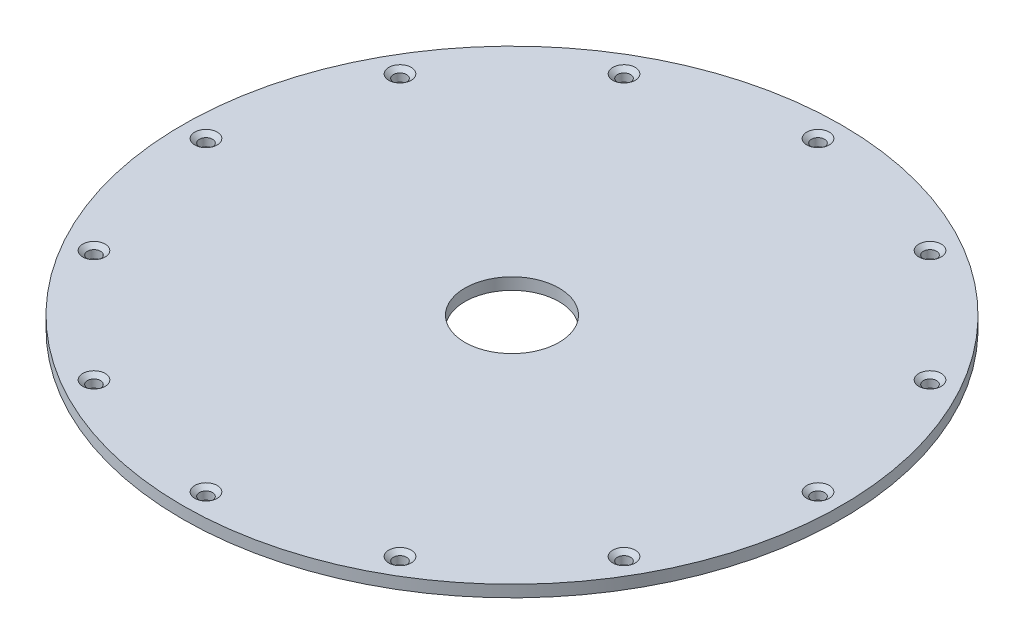
SolidWorks part; units mm, degrees
material "6063-T6"
ref_plane "Front Plane" through (0, 0, 0) normal (0, 0, 1) x (1, 0, 0)
ref_plane "Top Plane" through (0, 0, 0) normal (0, 1, 0) x (1, 0, 0)
ref_plane "Right Plane" through (0, 0, 0) normal (1, 0, 0) x (0, 0, -1)
ref_axis "Axis1" through (0, 55, 0) along (0, -1, 0)
sketch "Sketch1" plane through (0, 0, 0) normal (0, 0, 1) x (1, 0, 0)
  line L0 (-44.45, 0) -> (-6.35, 0)
  line L1 (0, 55) -> (0, -55) construction
  line L2 (-44.45, 0) -> (-44.45, 1.5875)
  line L3 (-44.45, 1.5875) -> (-6.35, 1.5875)
  line L4 (-44.45, 1.5875) -> (-6.35, 1.5875) construction
  line L5 (-6.35, 1.5875) -> (-6.35, 0)
  line L6 (-6.35, 0) -> (0, 0) construction
  line L7 (-44.45, 0) -> (-44.45, 1.5875) construction
  line L8 (-6.35, 1.5875) -> (-6.35, 0) construction
  point P1 (-6.35, 0)
  point P3 (-6.35, 8.9431)
  point P4 (-6.35, 1.5875)
  point P9 (0, 0)
  point P12 (-6.6434, 1.5875)
  point P13 (0, 0)
  point P16 (0, 0)
  point P17 (0, 0)
  point P18 (0, 0)
  point P19 (0, 0)
  point P21 (0, 0)
  point P22 (0, 0)
  point P23 (0, 0)
  point P24 (0, 0)
  point P25 (0, 0)
  point P26 (0, 0)
  point P28 (0, 0)
  point P29 (0, 0)
  point P30 (-6.6747, 0)
revolve "Revolve1" add sketch "Sketch1" angle 360 about axis through (0, 55, 0) along (0, -1, 0)
ref_plane "Hole Location Plane" through (0, 3.175, 0) normal (0, 1, 0) x (1, 0, 0)
sketch "Hole Location" plane through (0, 3.175, 0) normal (0, 1, 0) x (1, 0, 0)
  line L0 (0, 0) -> (-41.275, 0) construction
  circle A0 centre (0, 0) radius 41.275 construction
  dimension "D1" = 82.55
hole_wizard "CSK for #0 Flat Head Machine Screw (100)1" positions "Sketch4" profile "Sketch5" countersink size "#0" standard "ANSI Inch" end condition through all
sketch "Sketch4" plane through (0, 1.5875, 0) normal (0, 1, 0) x (1, 0, 0)
  point P0 (-41.275, 0)
sketch "Sketch5" plane through (-41.275, 1.5875, 0) normal (1, 0, 0) x (0, 0, 1)
  line L0 (0, 0) -> (0, 1.5875)
  line L1 (0, 1.5875) -> (0.889, 1.5875)
  line L2 (0.889, 1.5875) -> (0.889, 0.5222)
  line L3 (0.889, 0.5222) -> (1.5113, 0)
  line L5 (1.5113, 0) -> (0, 0)
  line L6 (-0.889, 0.5222) -> (-1.5113, 0) construction
  line L11 (0, -6.35) -> (0, 107.95) construction
  dimension "Thru Hole Dia." = 1.778
  dimension "Thru Hole Depth" = 1.5875
  dimension "Near C'Sink Dia." = 3.0226
  dimension "Near C'Sink Angle" = 100
pattern_circular "CirPattern1" count 12 every 30 about axis through (0, 0, 0) along (0, 1, 0) of "CSK for #0 Flat Head Machine Screw (100)1"
equation "\"D1@Hole Location\"=\"TANK DIAMETER@Cryo Tank.SLDASM\"+\"GASKET SEAT THICKNESS@Cryo Tank.SLDASM\""
